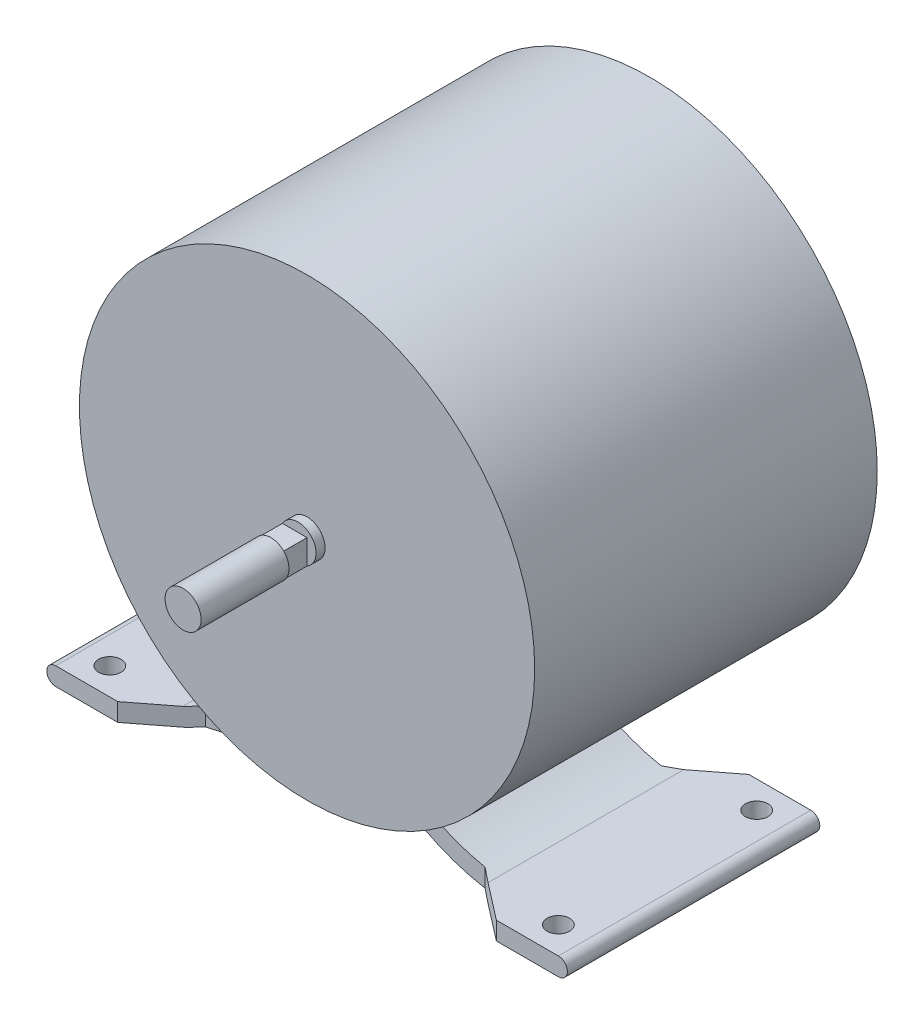
SolidWorks part; units mm, degrees
ref_plane "Ön Düzlem" through (0, 0, 0) normal (0, 0, 1) x (1, 0, 0)
ref_plane "Üst Düzlem" through (0, 0, 0) normal (0, 1, 0) x (1, 0, 0)
ref_plane "Sağ Düzlem" through (0, 0, 0) normal (1, 0, 0) x (0, 0, -1)
sketch "Sketch1" plane through (0, 0, 0) normal (0, 0, 1) x (1, 0, 0)
  circle A0 centre (0, 0) radius 50.5
  dimension "D1" = 101
extrude "Boss-Extrude1" add sketch "Sketch1" against normal blind 76
sketch "Sketch2" plane through (0, 0, 0) normal (0, 0, 1) x (1, 0, 0)
  circle A0 centre (0, 0) radius 4
  dimension "D1" = 8
extrude "Boss-Extrude2" add sketch "Sketch2" along normal blind 27.5
ref_plane "Plane1" through (0, 0, -82) normal (0, 0, -1) x (-1, 0, 0)
sketch "Sketch3" plane through (0, 0, -82) normal (0, 0, -1) x (-1, 0, 0)
  circle A0 centre (0, 0) radius 15.5
  dimension "D1" = 31
loft "Loft1" add profiles "Sketch3" section face at (50.5, 0, -76) section "Sketch3"
sketch "Sketch4" plane through (0, 0, 0) normal (0, 0, 1) x (1, 0, 0)
  line L8 (-55.75, -54.5) -> (-33.75, -54.5)
  line L9 (0, 33.8768) -> (0, 21.3587) construction
  line L10 (33.75, -54.5) -> (55.75, -54.5)
  line L11 (-55.75, -52.5) -> (-33.8675, -52.5)
  line L12 (33.8675, -52.5) -> (55.75, -52.5)
  line L13 (-55.75, -56.5) -> (-33.6352, -56.5)
  line L14 (33.6352, -56.5) -> (55.75, -56.5)
  arc A0 (-17.8336, -49.3782) -> (17.8336, -49.3782) centre (0, 0) ccw
  arc A1 (-33.75, -54.5) -> (-17.8336, -49.3782) centre (-38.7376, -11.7088) ccw
  arc A2 (33.75, -54.5) -> (17.8336, -49.3782) centre (38.7376, -11.7088) cw
  arc A3 (-33.8675, -52.5) -> (-18.0122, -47.1785) centre (-38.7376, -11.7088) ccw
  arc A4 (-18.0122, -47.1785) -> (18.0122, -47.1785) centre (0, 0) ccw
  arc A5 (33.8675, -52.5) -> (18.0122, -47.1785) centre (38.7376, -11.7088) cw
  arc A6 (-33.6352, -56.5) -> (-17.6607, -51.5592) centre (-38.7376, -11.7088) ccw
  arc A7 (-17.6607, -51.5592) -> (17.6607, -51.5592) centre (0, 0) ccw
  arc A8 (33.6352, -56.5) -> (17.6607, -51.5592) centre (38.7376, -11.7088) cw
  arc A9 (-55.75, -52.5) -> (-55.75, -56.5) centre (-55.75, -54.5) ccw
  arc A10 (55.75, -52.5) -> (55.75, -56.5) centre (55.75, -54.5) cw
  dimension "D1" = 105
  dimension "D2" = 54.5
  dimension "D3" = 2
  dimension "D4" = 22
  dimension "D5" = 22
  dimension "D6" = 33.75
  dimension "D7" = 2
extrude "Boss-Extrude3" add sketch "Sketch4" against normal blind 56 contours A3 A4 A5 L12 A10 L14 A8 A7 A6 L13 A9 L11
sketch "Sketch5" plane through (0, -56.5, 0) normal (0, -1, 0) x (1, 0, 0)
  line L0 (-31, -8.5) -> (31, -8.5)
  line L1 (31, -8.5) -> (42, 0)
  line L2 (33.6352, 0) -> (55.75, 0) construction
  line L3 (42, 0) -> (-42, 0)
  line L4 (-55.75, 0) -> (-33.6352, 0) construction
  line L5 (-42, 0) -> (-31, -8.5)
  line L6 (0, -56) -> (0, 0) construction
  line L7 (-57.75, -28) -> (57.75, -28) construction
  line L8 (-57.75, 0) -> (-57.75, -56) construction
  line L9 (57.75, -56) -> (57.75, 0) construction
  line L10 (-42, -56) -> (-31, -47.5)
  line L11 (42, -56) -> (-42, -56)
  line L12 (31, -47.5) -> (42, -56)
  line L13 (-31, -47.5) -> (31, -47.5)
  point P2 (0, -8.5)
  point P9 (0, 0)
  dimension "D1" = 8.5
  dimension "D2" = 84
  dimension "D3" = 62
extrude "Cut-Extrude1" cut sketch "Sketch5" against normal blind 14
sketch "Sketch6" plane through (0, 0, 0) normal (0, 0, 1) x (1, 0, 0)
  circle A0 centre (0, 0) radius 50.5
extrude "Boss-Extrude4" add sketch "Sketch6" against normal blind 69
sketch "Sketch7" plane through (0, -56.5, 0) normal (0, -1, 0) x (1, 0, 0)
  line L0 (0, -8.5) -> (0, -47.5) construction
  line L1 (18.0122, -8.5) -> (-18.0122, -8.5) construction
  line L2 (-17.6607, -47.5) -> (17.6607, -47.5) construction
  line L3 (57.75, -28) -> (-57.75, -28) construction
  line L4 (57.75, -56) -> (57.75, 0) construction
  line L5 (-57.75, 0) -> (-57.75, -56) construction
  line L6 (-55.75, 0) -> (-42, 0) construction
  circle A0 centre (-49.75, -6) radius 2.5
  circle A1 centre (-49.75, -50) radius 2.5
  circle A2 centre (49.75, -50) radius 2.5
  circle A3 centre (49.75, -6) radius 2.5
  dimension "D3" = 5
  dimension "D1" = 6
  dimension "D2" = 8
extrude "Cut-Extrude2" cut sketch "Sketch7" against normal up to next
sketch "Sketch8" plane through (170.8346, -107.1628, -173.5) normal (1, 0, 0) x (0, 0, -1)
  line L0 (-175.5, 111.1628) -> (-175.5, 109.1628)
  line L1 (-173.5, 111.1628) -> (-201, 111.1628) construction
  line L2 (-175.5, 109.1628) -> (-181.5, 109.1628)
  line L3 (-181.5, 109.1628) -> (-181.5, 111.1628)
  line L4 (-181.5, 111.1628) -> (-175.5, 111.1628)
  line L5 (-173.5, 157.6628) -> (-173.5, 56.6628) construction
  dimension "D1" = 2
  dimension "D2" = 6
  dimension "D3" = 2
extrude "Cut-Extrude3" cut sketch "Sketch8" against normal through all both and the other way through all
pattern_circular "CirPattern1" count 2 over 90 about axis through (0, 0, 27.5) along (0, 0, -1) of "Cut-Extrude3"
